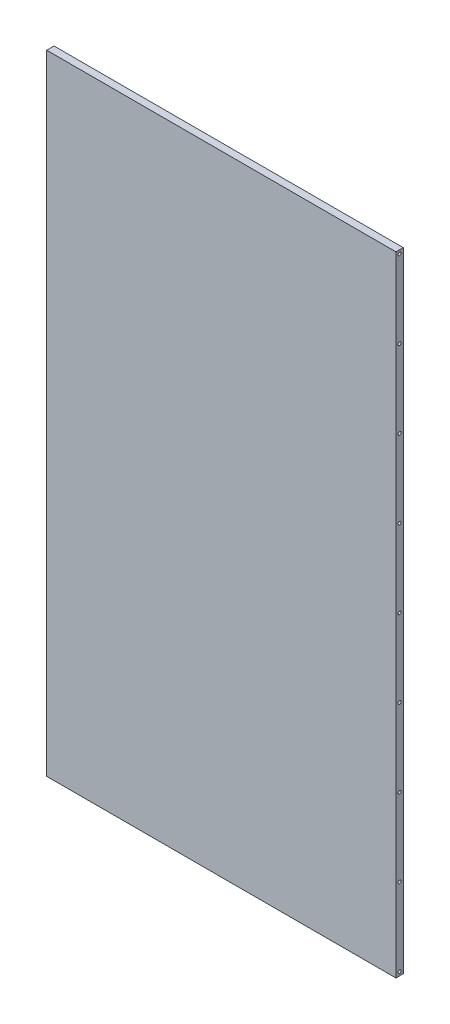
SolidWorks part; units mm, degrees
ref_plane "Front" through (0, 0, 0) normal (0, 0, 1) x (1, 0, 0)
ref_plane "Top" through (0, 0, 0) normal (0, 1, 0) x (1, 0, 0)
ref_plane "Right" through (0, 0, 0) normal (1, 0, 0) x (0, 0, -1)
sketch "Sketch1" plane through (0, 0, 0) normal (0, 0, 1) x (1, 0, 0)
  line L1 (0, 0) -> (286.0056, 0)
  line L2 (0, 0) -> (0, 515)
  line L3 (0, 515) -> (286.0056, 515)
  line L4 (286.0056, 0) -> (286.0056, 515)
  dimension "D1" = 286.0056
  dimension "D2" = 515
extrude "Boss-Extrude1" add sketch "Sketch1" along normal blind 5.9944
hole_wizard "Tap Drill for M3x0.5 Tap1" positions "Sketch3" profile "Sketch2" hole size "M3x0.5" standard "ANSI Metric"
sketch "Sketch3" plane through (286.0056, 0, 0) normal (1, 0, 0) x (0, 0, -1)
  line L0 (-2.9972, 0) -> (-2.9972, 515) construction
  line L1 (-5.9944, 0) -> (0, 0) construction
  line L2 (-5.9944, 515) -> (0, 515) construction
  point P0 (-2.9972, 257.5)
sketch "Sketch2" plane through (286.0056, 257.5, 2.9972) normal (0, 1, 0) x (0, 0, -1)
  line L0 (0, 0) -> (0, 30.7511)
  line L1 (0, 30.7511) -> (1.25, 30)
  line L2 (1.25, 30) -> (1.25, 0)
  line L5 (1.25, 0) -> (0, 0)
  line L10 (0, 30.7511) -> (-1.25, 30) construction
  line L11 (0, -6.35) -> (0, 107.95) construction
  dimension "Hole Dia." = 2.5
  dimension "Hole Depth" = 30
  dimension "Drill Angle" = 118
pattern_linear "LPattern1" count 5 spacing 63.625 along (0, 1, 0) count 5 spacing 63.625 along (0, -1, 0) of "Tap Drill for M3x0.5 Tap1"
ref_plane "Plane1" through (143.0028, 0, 0) normal (1, 0, 0) x (0, 0, -1)
mirror "Mirror1" about plane through (143.0028, 0, 0) normal (1, 0, 0) of "LPattern1", "Tap Drill for M3x0.5 Tap1"
equation "\"ABS_thickness_1/16\" = 1.524\t"
equation "\"ABS_thickness_3/32\" = 2.3622"
equation "\"ABS_thickness_1/8\" = 2.9972\t"
equation "\"ABS_thickness_1/4\" = 5.9944"
equation "\"Bus_bar_thickness\" = 3.175"
equation "\"Connector_width\" = 20.2"
equation "\"Number_of_cells_long\" = 25"
equation "\"Number_of_cells_wide\" = 2"
equation "\"Cell_height\" = 65.0"
equation "\"Cell_diam\" = 18.0"
equation "\"Enclosure_Width\" = 292"
equation "\"Enclosure_Length\" = 260"
equation "\"Enclosure_Height\" = 515"
equation "\"D2@Sketch1\"=\"Enclosure_Height\""
equation "\"D1@Sketch1\"=\"Enclosure_Width\"-2*\"ABS_thickness_1/8\""
equation "\"D1@Boss-Extrude1\"=\"ABS_thickness_1/4\""
equation "\"D3@LPattern1\"=(\"Enclosure_Height\"-6)/8"
equation "\"D4@LPattern1\"=(\"Enclosure_Height\"-6)/8"
